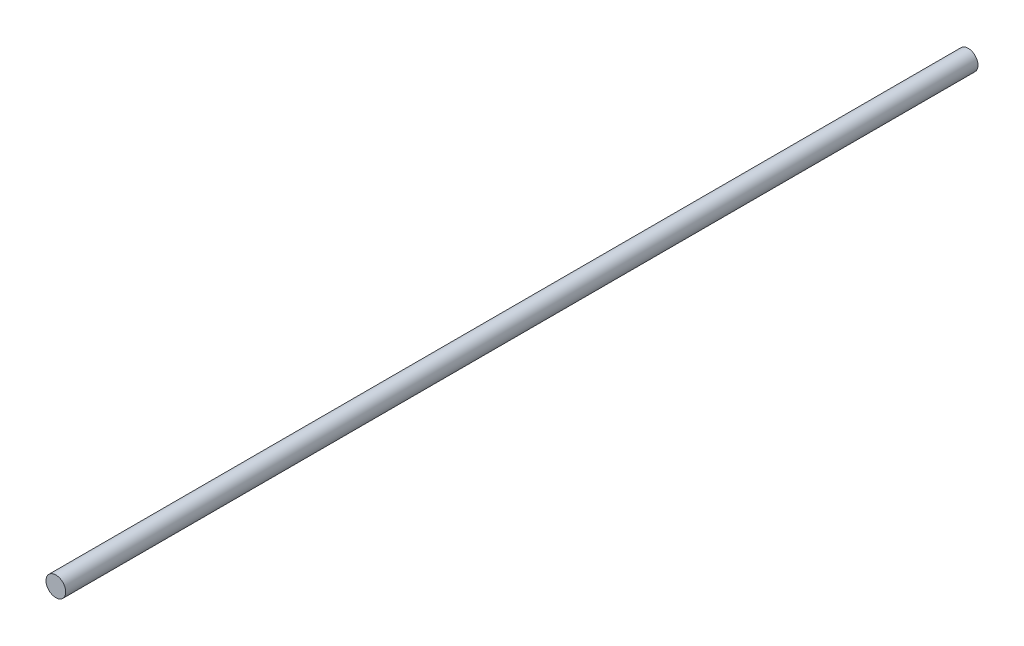
SolidWorks part; units mm, degrees
material "AISI 304"
ref_plane "Plano frontal" through (0, 0, 0) normal (0, 0, 1) x (1, 0, 0)
ref_plane "Plano superior" through (0, 0, 0) normal (0, 1, 0) x (1, 0, 0)
ref_plane "Plano direito" through (0, 0, 0) normal (1, 0, 0) x (0, 0, -1)
sketch "Esboço1" plane through (0, 0, 0) normal (0, 0, 1) x (1, 0, 0)
  circle A0 centre (0, 0) radius 4
  dimension "D1" = 8
extrude "Ressalto-extrusão1" add sketch "Esboço1" along normal blind 370
